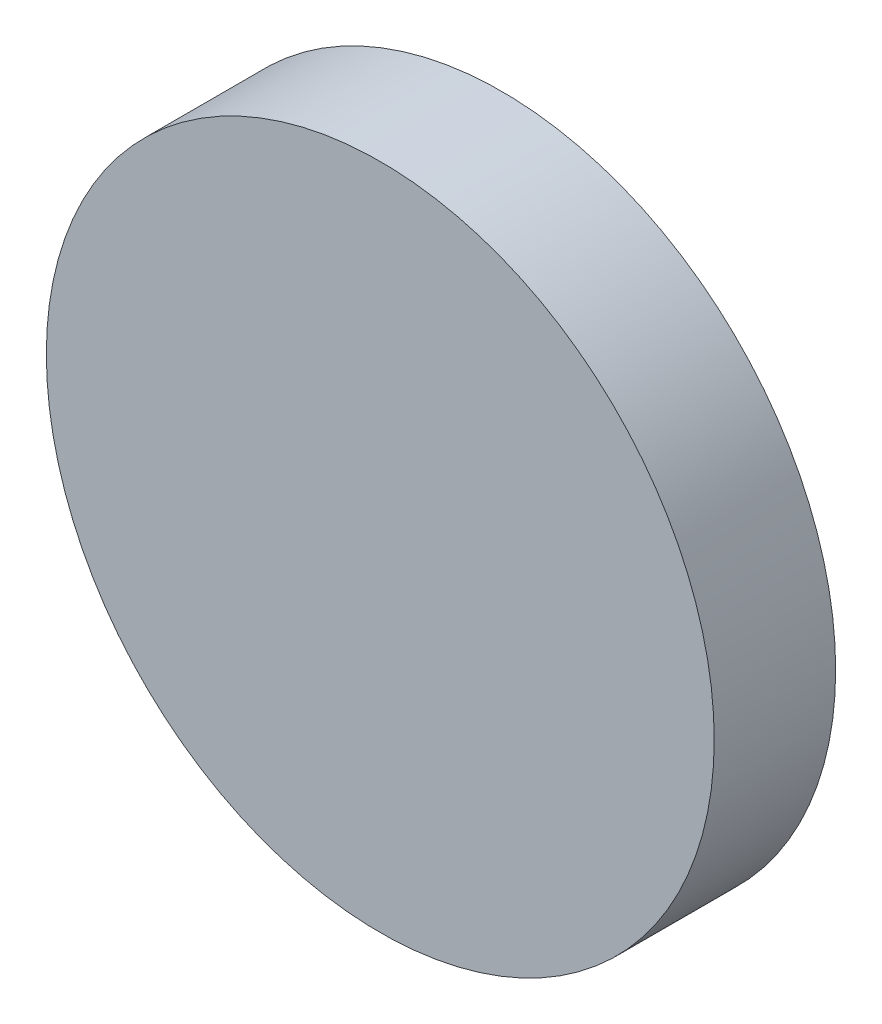
SolidWorks part; units mm, degrees
ref_plane "Front Plane" through (0, 0, 0) normal (0, 0, 1) x (1, 0, 0)
ref_plane "Top Plane" through (0, 0, 0) normal (0, 1, 0) x (1, 0, 0)
ref_plane "Right Plane" through (0, 0, 0) normal (1, 0, 0) x (0, 0, -1)
sketch "Sketch1" plane through (0, 0, 0) normal (0, 0, 1) x (1, 0, 0)
  circle A0 centre (0, 0) radius 139.7
  dimension "D1" = 279.4
extrude "Boss-Extrude1" add sketch "Sketch1" along normal mid plane 50.8
